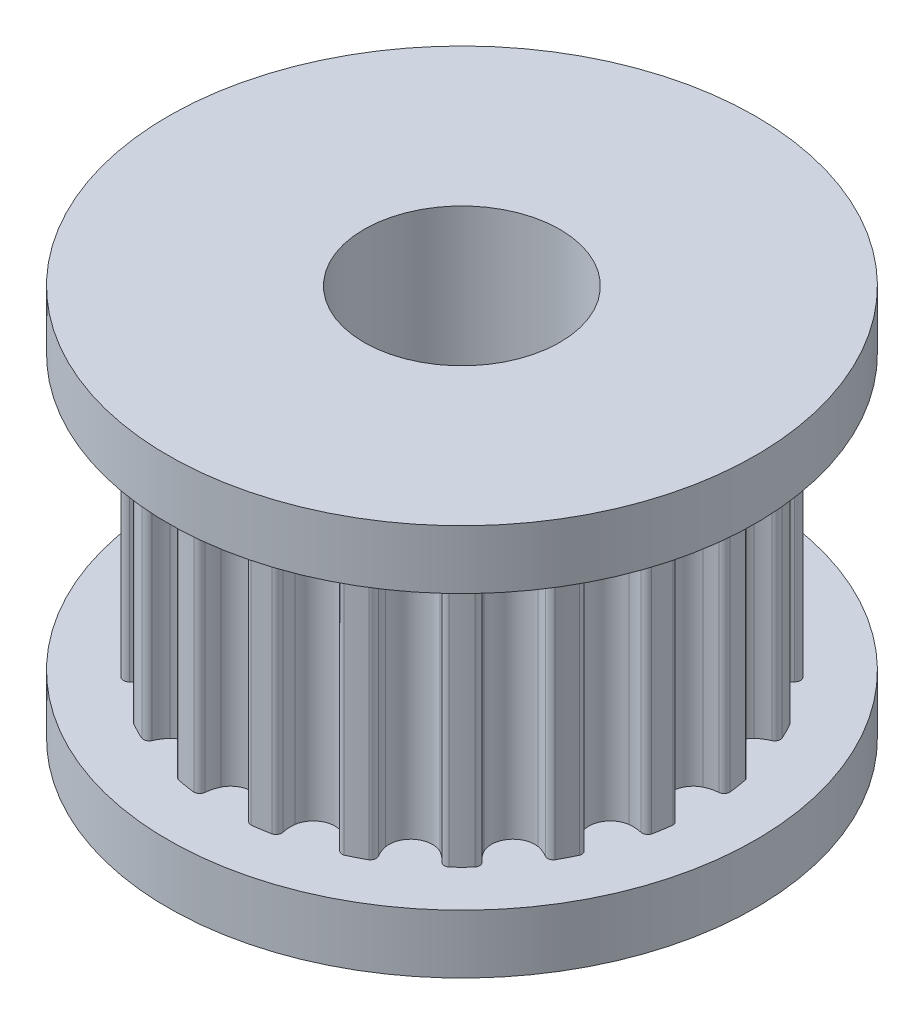
SolidWorks part; units mm, degrees
ref_plane "Front" through (0, 0, 0) normal (0, 0, 1) x (1, 0, 0)
ref_plane "Top" through (0, 0, 0) normal (0, 1, 0) x (1, 0, 0)
ref_plane "Right" through (0, 0, 0) normal (1, 0, 0) x (0, 0, -1)
sketch "Sketch1" plane through (0, 0, 0) normal (0, 0, 1) x (1, 0, 0)
  line L0 (0, 0) -> (0, 10) construction
  line L1 (2.5, 0) -> (2.5, 10)
  line L2 (2.5, 10) -> (7.5, 10)
  line L3 (7.5, 10) -> (7.5, 8.5)
  line L4 (7.5, 8.5) -> (6.3662, 8.5)
  line L5 (6.3662, 8.5) -> (6.3662, 1.5)
  line L6 (6.3662, 1.5) -> (7.5, 1.5)
  line L7 (7.5, 1.5) -> (7.5, 0)
  line L8 (7.5, 0) -> (2.5, 0)
  dimension "D1" = 10
  dimension "D3" = 15
  dimension "D4" = 12.7324
  dimension "D5" = 5
  dimension "D2" = 1.5
revolve "Revolve1" add sketch "Sketch1" angle 360 about L0
sketch "Sketch2" plane through (0, 1.5, 0) normal (0, 1, 0) x (1, 0, 0)
  circle A0 centre (0, 0) radius 6.3662 construction
  circle A1 centre (0, 0) radius 6.3662
  circle A3 centre (0, 0) radius 4.3662
  dimension "D1" = 2
extrude "Cut-Extrude1" cut sketch "Sketch2" along normal up to surface (7 mm away) up to face at (0, 8.5, -7.5)
sketch "Sketch3" plane through (0, 1.5, 0) normal (0, 1, 0) x (1, 0, 0)
  circle A0 centre (0, 0) radius 1.5
  arc A1 (6.1135, -0.7303) -> (5.9829, -0.5816) centre (5.9635, -0.7303) ccw
  arc A2 (5.659, -0.4964) -> (5.9829, -0.5816) centre (6.0717, 0.4144) ccw
  arc A3 (5.3522, 0) -> (5.659, -0.4964) centre (5.9072, 0) ccw
  arc A4 (5.659, 0.4964) -> (5.3522, 0) centre (5.9072, 0) ccw
  arc A5 (5.9829, 0.5816) -> (5.659, 0.4964) centre (6.0717, -0.4144) ccw
  arc A6 (5.9829, 0.5816) -> (6.1135, 0.7303) centre (5.9635, 0.7303) ccw
  arc A7 (6.1135, 0.7303) -> (6.0399, 1.1946) centre (0.0442, 0.007) ccw
  arc A8 (6.0399, 1.1946) -> (5.8698, 1.2957) centre (5.8973, 1.1482) ccw
  arc A9 (5.5354, 1.2766) -> (5.8698, 1.2957) centre (5.6465, 2.2704) ccw
  arc A10 (5.0902, 1.6539) -> (5.5354, 1.2766) centre (5.6181, 1.8254) ccw
  arc A11 (5.2286, 2.2208) -> (5.0902, 1.6539) centre (5.6181, 1.8254) ccw
  arc A12 (5.5103, 2.4019) -> (5.2286, 2.2208) centre (5.9026, 1.4821) ccw
  arc A13 (5.5103, 2.4019) -> (5.5886, 2.5838) centre (5.4459, 2.5374) ccw
  arc A14 (5.5886, 2.5838) -> (5.3752, 3.0025) centre (0.0399, 0.0203) ccw
  arc A15 (5.3752, 3.0025) -> (5.1821, 3.0461) centre (5.2538, 2.9144) ccw
  arc A16 (4.87, 2.9247) -> (5.1821, 3.0461) centre (4.6685, 3.9042) ccw
  arc A17 (4.33, 3.1459) -> (4.87, 2.9247) centre (4.779, 3.4722) ccw
  arc A18 (4.2864, 3.7279) -> (4.33, 3.1459) centre (4.779, 3.4722) ccw
  arc A19 (4.4984, 3.9872) -> (4.2864, 3.7279) centre (5.1557, 3.2336) ccw
  arc A20 (4.4984, 3.9872) -> (4.5166, 4.1843) centre (4.3953, 4.0961) ccw
  arc A21 (4.5166, 4.1843) -> (4.1843, 4.5166) centre (0.0317, 0.0317) ccw
  arc A22 (4.1843, 4.5166) -> (3.9872, 4.4984) centre (4.0961, 4.3953) ccw
  arc A23 (3.7279, 4.2864) -> (3.9872, 4.4984) centre (3.2336, 5.1557) ccw
  arc A24 (3.1459, 4.33) -> (3.7279, 4.2864) centre (3.4722, 4.779) ccw
  arc A25 (2.9247, 4.87) -> (3.1459, 4.33) centre (3.4722, 4.779) ccw
  arc A26 (3.0461, 5.1821) -> (2.9247, 4.87) centre (3.9042, 4.6685) ccw
  arc A27 (3.0461, 5.1821) -> (3.0025, 5.3752) centre (2.9144, 5.2538) ccw
  arc A28 (3.0025, 5.3752) -> (2.5838, 5.5886) centre (0.0203, 0.0399) ccw
  arc A29 (2.5838, 5.5886) -> (2.4019, 5.5103) centre (2.5374, 5.4459) ccw
  arc A30 (2.2208, 5.2286) -> (2.4019, 5.5103) centre (1.4821, 5.9026) ccw
  arc A31 (1.6539, 5.0902) -> (2.2208, 5.2286) centre (1.8254, 5.6181) ccw
  arc A32 (1.2766, 5.5354) -> (1.6539, 5.0902) centre (1.8254, 5.6181) ccw
  arc A33 (1.2957, 5.8698) -> (1.2766, 5.5354) centre (2.2704, 5.6465) ccw
  arc A34 (1.2957, 5.8698) -> (1.1946, 6.0399) centre (1.1482, 5.8973) ccw
  arc A35 (1.1946, 6.0399) -> (0.7303, 6.1135) centre (0.007, 0.0442) ccw
  arc A36 (0.7303, 6.1135) -> (0.5816, 5.9829) centre (0.7303, 5.9635) ccw
  arc A37 (0.4964, 5.659) -> (0.5816, 5.9829) centre (-0.4144, 6.0717) ccw
  arc A38 (0, 5.3522) -> (0.4964, 5.659) centre (0, 5.9072) ccw
  arc A39 (-0.4964, 5.659) -> (0, 5.3522) centre (0, 5.9072) ccw
  arc A40 (-0.5816, 5.9829) -> (-0.4964, 5.659) centre (0.4144, 6.0717) ccw
  arc A41 (-0.5816, 5.9829) -> (-0.7303, 6.1135) centre (-0.7303, 5.9635) ccw
  arc A42 (-0.7303, 6.1135) -> (-1.1946, 6.0399) centre (-0.007, 0.0442) ccw
  arc A43 (-1.1946, 6.0399) -> (-1.2957, 5.8698) centre (-1.1482, 5.8973) ccw
  arc A44 (-1.2766, 5.5354) -> (-1.2957, 5.8698) centre (-2.2704, 5.6465) ccw
  arc A45 (-1.6539, 5.0902) -> (-1.2766, 5.5354) centre (-1.8254, 5.6181) ccw
  arc A46 (-2.2208, 5.2286) -> (-1.6539, 5.0902) centre (-1.8254, 5.6181) ccw
  arc A47 (-2.4019, 5.5103) -> (-2.2208, 5.2286) centre (-1.4821, 5.9026) ccw
  arc A48 (-2.4019, 5.5103) -> (-2.5838, 5.5886) centre (-2.5374, 5.4459) ccw
  arc A49 (-2.5838, 5.5886) -> (-3.0025, 5.3752) centre (-0.0203, 0.0399) ccw
  arc A50 (-3.0025, 5.3752) -> (-3.0461, 5.1821) centre (-2.9144, 5.2538) ccw
  arc A51 (-2.9247, 4.87) -> (-3.0461, 5.1821) centre (-3.9042, 4.6685) ccw
  arc A52 (-3.1459, 4.33) -> (-2.9247, 4.87) centre (-3.4722, 4.779) ccw
  arc A53 (-3.7279, 4.2864) -> (-3.1459, 4.33) centre (-3.4722, 4.779) ccw
  arc A54 (-3.9872, 4.4984) -> (-3.7279, 4.2864) centre (-3.2336, 5.1557) ccw
  arc A55 (-3.9872, 4.4984) -> (-4.1843, 4.5166) centre (-4.0961, 4.3953) ccw
  arc A56 (-4.1843, 4.5166) -> (-4.5166, 4.1843) centre (-0.0317, 0.0317) ccw
  arc A57 (-4.5166, 4.1843) -> (-4.4984, 3.9872) centre (-4.3953, 4.0961) ccw
  arc A58 (-4.2864, 3.7279) -> (-4.4984, 3.9872) centre (-5.1557, 3.2336) ccw
  arc A59 (-4.33, 3.1459) -> (-4.2864, 3.7279) centre (-4.779, 3.4722) ccw
  arc A60 (-4.87, 2.9247) -> (-4.33, 3.1459) centre (-4.779, 3.4722) ccw
  arc A61 (-5.1821, 3.0461) -> (-4.87, 2.9247) centre (-4.6685, 3.9042) ccw
  arc A62 (-5.1821, 3.0461) -> (-5.3752, 3.0025) centre (-5.2538, 2.9144) ccw
  arc A63 (-5.3752, 3.0025) -> (-5.5886, 2.5838) centre (-0.0399, 0.0203) ccw
  arc A64 (-5.5886, 2.5838) -> (-5.5103, 2.4019) centre (-5.4459, 2.5374) ccw
  arc A65 (-5.2286, 2.2208) -> (-5.5103, 2.4019) centre (-5.9026, 1.4821) ccw
  arc A66 (-5.0902, 1.6539) -> (-5.2286, 2.2208) centre (-5.6181, 1.8254) ccw
  arc A67 (-5.5354, 1.2766) -> (-5.0902, 1.6539) centre (-5.6181, 1.8254) ccw
  arc A68 (-5.8698, 1.2957) -> (-5.5354, 1.2766) centre (-5.6465, 2.2704) ccw
  arc A69 (-5.8698, 1.2957) -> (-6.0399, 1.1946) centre (-5.8973, 1.1482) ccw
  arc A70 (-6.0399, 1.1946) -> (-6.1135, 0.7303) centre (-0.0442, 0.007) ccw
  arc A71 (-6.1135, 0.7303) -> (-5.9829, 0.5816) centre (-5.9635, 0.7303) ccw
  arc A72 (-5.659, 0.4964) -> (-5.9829, 0.5816) centre (-6.0717, -0.4144) ccw
  arc A73 (-5.3522, 0) -> (-5.659, 0.4964) centre (-5.9072, 0) ccw
  arc A74 (-5.659, -0.4964) -> (-5.3522, 0) centre (-5.9072, 0) ccw
  arc A75 (-5.9829, -0.5816) -> (-5.659, -0.4964) centre (-6.0717, 0.4144) ccw
  arc A76 (-5.9829, -0.5816) -> (-6.1135, -0.7303) centre (-5.9635, -0.7303) ccw
  arc A77 (-6.1135, -0.7303) -> (-6.0399, -1.1946) centre (-0.0442, -0.007) ccw
  arc A78 (-6.0399, -1.1946) -> (-5.8698, -1.2957) centre (-5.8973, -1.1482) ccw
  arc A79 (-5.5354, -1.2766) -> (-5.8698, -1.2957) centre (-5.6465, -2.2704) ccw
  arc A80 (-5.0902, -1.6539) -> (-5.5354, -1.2766) centre (-5.6181, -1.8254) ccw
  arc A81 (-5.2286, -2.2208) -> (-5.0902, -1.6539) centre (-5.6181, -1.8254) ccw
  arc A82 (-5.5103, -2.4019) -> (-5.2286, -2.2208) centre (-5.9026, -1.4821) ccw
  arc A83 (-5.5103, -2.4019) -> (-5.5886, -2.5838) centre (-5.4459, -2.5374) ccw
  arc A84 (-5.5886, -2.5838) -> (-5.3752, -3.0025) centre (-0.0399, -0.0203) ccw
  arc A85 (-5.3752, -3.0025) -> (-5.1821, -3.0461) centre (-5.2538, -2.9144) ccw
  arc A86 (-4.87, -2.9247) -> (-5.1821, -3.0461) centre (-4.6685, -3.9042) ccw
  arc A87 (-4.33, -3.1459) -> (-4.87, -2.9247) centre (-4.779, -3.4722) ccw
  arc A88 (-4.2864, -3.7279) -> (-4.33, -3.1459) centre (-4.779, -3.4722) ccw
  arc A89 (-4.4984, -3.9872) -> (-4.2864, -3.7279) centre (-5.1557, -3.2336) ccw
  arc A90 (-4.4984, -3.9872) -> (-4.5166, -4.1843) centre (-4.3953, -4.0961) ccw
  arc A91 (-4.5166, -4.1843) -> (-4.1843, -4.5166) centre (-0.0317, -0.0317) ccw
  arc A92 (-4.1843, -4.5166) -> (-3.9872, -4.4984) centre (-4.0961, -4.3953) ccw
  arc A93 (-3.7279, -4.2864) -> (-3.9872, -4.4984) centre (-3.2336, -5.1557) ccw
  arc A94 (-3.1459, -4.33) -> (-3.7279, -4.2864) centre (-3.4722, -4.779) ccw
  arc A95 (-2.9247, -4.87) -> (-3.1459, -4.33) centre (-3.4722, -4.779) ccw
  arc A96 (-3.0461, -5.1821) -> (-2.9247, -4.87) centre (-3.9042, -4.6685) ccw
  arc A97 (-3.0461, -5.1821) -> (-3.0025, -5.3752) centre (-2.9144, -5.2538) ccw
  arc A98 (-3.0025, -5.3752) -> (-2.5838, -5.5886) centre (-0.0203, -0.0399) ccw
  arc A99 (-2.5838, -5.5886) -> (-2.4019, -5.5103) centre (-2.5374, -5.4459) ccw
  arc A100 (-2.2208, -5.2286) -> (-2.4019, -5.5103) centre (-1.4821, -5.9026) ccw
  arc A101 (-1.6539, -5.0902) -> (-2.2208, -5.2286) centre (-1.8254, -5.6181) ccw
  arc A102 (-1.2766, -5.5354) -> (-1.6539, -5.0902) centre (-1.8254, -5.6181) ccw
  arc A103 (-1.2957, -5.8698) -> (-1.2766, -5.5354) centre (-2.2704, -5.6465) ccw
  arc A104 (-1.2957, -5.8698) -> (-1.1946, -6.0399) centre (-1.1482, -5.8973) ccw
  arc A105 (-1.1946, -6.0399) -> (-0.7303, -6.1135) centre (-0.007, -0.0442) ccw
  arc A106 (-0.7303, -6.1135) -> (-0.5816, -5.9829) centre (-0.7303, -5.9635) ccw
  arc A107 (-0.4964, -5.659) -> (-0.5816, -5.9829) centre (0.4144, -6.0717) ccw
  arc A108 (0, -5.3522) -> (-0.4964, -5.659) centre (0, -5.9072) ccw
  arc A109 (0.4964, -5.659) -> (0, -5.3522) centre (0, -5.9072) ccw
  arc A110 (0.5816, -5.9829) -> (0.4964, -5.659) centre (-0.4144, -6.0717) ccw
  arc A111 (0.5816, -5.9829) -> (0.7303, -6.1135) centre (0.7303, -5.9635) ccw
  arc A112 (0.7303, -6.1135) -> (1.1946, -6.0399) centre (0.007, -0.0442) ccw
  arc A113 (1.1946, -6.0399) -> (1.2957, -5.8698) centre (1.1482, -5.8973) ccw
  arc A114 (1.2766, -5.5354) -> (1.2957, -5.8698) centre (2.2704, -5.6465) ccw
  arc A115 (1.6539, -5.0902) -> (1.2766, -5.5354) centre (1.8254, -5.6181) ccw
  arc A116 (2.2208, -5.2286) -> (1.6539, -5.0902) centre (1.8254, -5.6181) ccw
  arc A117 (2.4019, -5.5103) -> (2.2208, -5.2286) centre (1.4821, -5.9026) ccw
  arc A118 (2.4019, -5.5103) -> (2.5838, -5.5886) centre (2.5374, -5.4459) ccw
  arc A119 (2.5838, -5.5886) -> (3.0025, -5.3752) centre (0.0203, -0.0399) ccw
  arc A120 (3.0025, -5.3752) -> (3.0461, -5.1821) centre (2.9144, -5.2538) ccw
  arc A121 (2.9247, -4.87) -> (3.0461, -5.1821) centre (3.9042, -4.6685) ccw
  arc A122 (3.1459, -4.33) -> (2.9247, -4.87) centre (3.4722, -4.779) ccw
  arc A123 (3.7279, -4.2864) -> (3.1459, -4.33) centre (3.4722, -4.779) ccw
  arc A124 (3.9872, -4.4984) -> (3.7279, -4.2864) centre (3.2336, -5.1557) ccw
  arc A125 (3.9872, -4.4984) -> (4.1843, -4.5166) centre (4.0961, -4.3953) ccw
  arc A126 (4.1843, -4.5166) -> (4.5166, -4.1843) centre (0.0317, -0.0317) ccw
  arc A127 (4.5166, -4.1843) -> (4.4984, -3.9872) centre (4.3953, -4.0961) ccw
  arc A128 (4.2864, -3.7279) -> (4.4984, -3.9872) centre (5.1557, -3.2336) ccw
  arc A129 (4.33, -3.1459) -> (4.2864, -3.7279) centre (4.779, -3.4722) ccw
  arc A130 (4.87, -2.9247) -> (4.33, -3.1459) centre (4.779, -3.4722) ccw
  arc A131 (5.1821, -3.0461) -> (4.87, -2.9247) centre (4.6685, -3.9042) ccw
  arc A132 (5.1821, -3.0461) -> (5.3752, -3.0025) centre (5.2538, -2.9144) ccw
  arc A133 (5.3752, -3.0025) -> (5.5886, -2.5838) centre (0.0399, -0.0203) ccw
  arc A134 (5.5886, -2.5838) -> (5.5103, -2.4019) centre (5.4459, -2.5374) ccw
  arc A135 (5.2286, -2.2208) -> (5.5103, -2.4019) centre (5.9026, -1.4821) ccw
  arc A136 (5.0902, -1.6539) -> (5.2286, -2.2208) centre (5.6181, -1.8254) ccw
  arc A137 (5.5354, -1.2766) -> (5.0902, -1.6539) centre (5.6181, -1.8254) ccw
  arc A138 (5.8698, -1.2957) -> (5.5354, -1.2766) centre (5.6465, -2.2704) ccw
  arc A139 (5.8698, -1.2957) -> (6.0399, -1.1946) centre (5.8973, -1.1482) ccw
  arc A140 (6.0399, -1.1946) -> (6.1135, -0.7303) centre (0.0442, -0.007) ccw
  circle A141 centre (0, 0) radius 4.3662 construction
  circle A142 centre (0, 0) radius 4.3662
extrude "Boss-Extrude1" add sketch "Sketch3" along normal up to surface (7 mm away) contours A139 A140 A1 A2 A3 A4 A5 A6 A7 A8 A9 A10 A11 A12 A13 A14 A15 A16 A17 A18 A19 A20 A21 A22 A23 A24 A25 A26 A27 A28 A29 A30 A31 A32 A33 A34 A35 A36 A37 A38 A39 A40 A41 A42 A43 A44 A45 A46 A47 A48 A49
equation "\"D4@Sketch1\"=20*2/3.14159"
